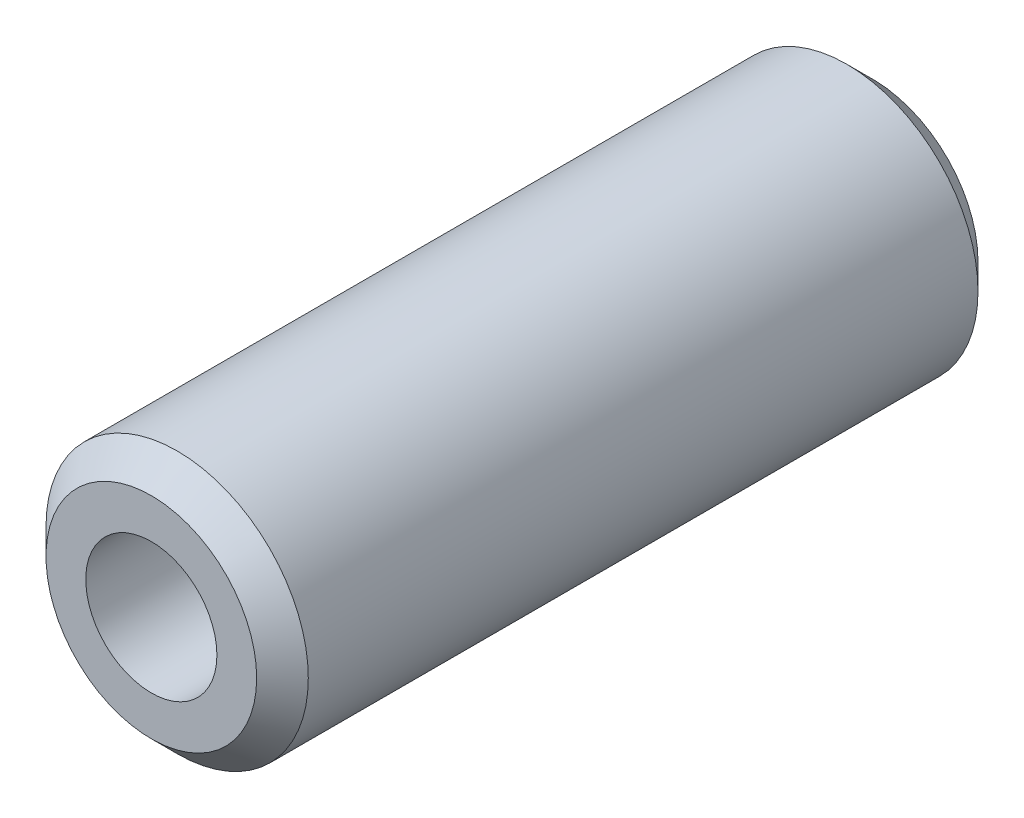
SolidWorks part; units mm, degrees
ref_plane "Plan de face" through (0, 0, 0) normal (0, 0, 1) x (1, 0, 0)
ref_plane "Plan de dessus" through (0, 0, 0) normal (0, 1, 0) x (1, 0, 0)
ref_plane "Plan de droite" through (0, 0, 0) normal (1, 0, 0) x (0, 0, -1)
sketch "Esquisse1" plane through (0, 0, 0) normal (0, 0, 1) x (1, 0, 0)
  circle A0 centre (0, 0) radius 6.35
  circle A1 centre (0, 0) radius 12.7
  dimension "D1" = 12.7
  dimension "D2" = 25.4
extrude "Boss.-Extru.1" add sketch "Esquisse1" along normal mid plane 69.85
chamfer "Chanfrein1" distance 2.5 angle 45 2 edges at (12.7, 0, -34.925) (12.7, 0, 34.925)
